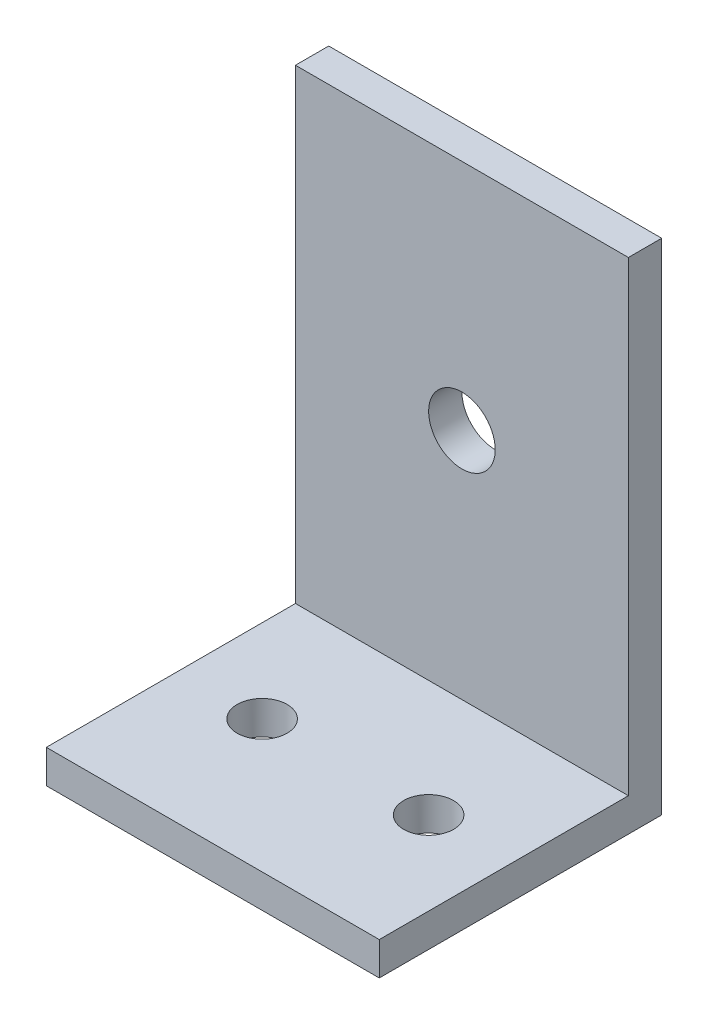
SolidWorks part; units mm, degrees
material "6063-O"
ref_plane "Front" through (0, 0, 0) normal (0, 0, 1) x (1, 0, 0)
ref_plane "Top" through (0, 0, 0) normal (0, 1, 0) x (1, 0, 0)
ref_plane "Right" through (0, 0, 0) normal (1, 0, 0) x (0, 0, -1)
sketch "草图1" plane through (0, 0, 0) normal (1, 0, 0) x (0, 0, -1)
  line L0 (0, 0) -> (0, 35)
  line L1 (0, 35) -> (3, 35)
  line L2 (3, 35) -> (3, -3)
  line L3 (0, 0) -> (-35, 0)
  line L4 (-35, 0) -> (-35, -3)
  line L5 (-35, -3) -> (3, -3)
  dimension "D1" = 35
  dimension "D2" = 3
  dimension "D3" = 38
  dimension "D4" = 35
extrude "凸台-拉伸1" add sketch "草图1" along normal blind 30
sketch "草图5" plane through (0, 0, 0) normal (0, 0, 1) x (1, 0, 0)
  line L0 (0, 20) -> (15, 35)
  line L1 (0, 35) -> (0, 0) construction
  line L2 (30, 35) -> (0, 35) construction
  line L3 (15, 35) -> (30, 20)
  line L4 (30, 35) -> (30, 0) construction
  line L5 (30, 20) -> (30, 35)
  line L6 (30, 35) -> (0, 35)
  line L7 (0, 35) -> (0, 20)
  line L8 (7.5, 27.5) -> (22.5, 27.5)
  line M3 (0, 35) -> (0, 0)
  line M5 (30, 0) -> (30, 35)
  line M6 (30, 35) -> (0, 35)
  dimension "D1" = 15
extrude "切除-拉伸4" [suppressed] cut sketch "草图5" against normal through all and the other way through all contours L0 M3 M6 | L0 L8 L3 | L3 M6 M5
fillet "圆角1" [suppressed] radius 3
sketch "草图6" plane through (0, 0, 0) normal (-1, 0, 0) x (0, 0, 1)
  line L1 (13.9641, -6.0203) -> (-8.0349, -6.0203)
  line L2 (13.9641, -6.0203) -> (13.9641, 37.9578)
  line L3 (13.9641, 37.9578) -> (-8.0349, 37.9578)
  line L4 (-8.0349, -6.0203) -> (-8.0349, 37.9578)
extrude "切除-拉伸5" cut sketch "草图6" against normal blind 10
sketch "草图7" plane through (0, 0, 0) normal (0, 1, 0) x (1, 0, 0)
  line L0 (0, -13.9641) -> (0, -35) construction
  line L1 (0, -13.9641) -> (30, -13.9641)
  line L2 (0, -13.9641) -> (0, -35)
  line L3 (0, -35) -> (30, -35)
  line L4 (30, -13.9641) -> (30, -35)
  line L5 (10, -13.9641) -> (0, -13.9641) construction
  line L6 (30, 0) -> (30, -35) construction
extrude "切除-拉伸6" cut sketch "草图7" against normal blind 10
sketch "草图8" plane through (0, 0, 0) normal (0, 1, 0) x (1, 0, 0)
  line L0 (10, -13.9641) -> (10, 0) construction
  line L3 (30, 0) -> (10, 0) construction
  circle A0 centre (15, -6) radius 1.5
  circle A1 centre (25, -6) radius 1.5
  dimension "D2" = 5
  dimension "D4" = 3
  dimension "D5" = 3
  dimension "D1" = 10
  dimension "D3" = 6
extrude "切除-拉伸7" cut sketch "草图8" against normal blind 10
sketch "草图9" plane through (0, 0, 0) normal (0, 1, 0) x (1, 0, 0)
  line L0 (10, -13.9641) -> (10, 0) construction
  line L1 (10, -13.9641) -> (30, -13.9641)
  line L2 (10, -13.9641) -> (10, 0)
  line L3 (10, 0) -> (30, 0)
  line L4 (30, -13.9641) -> (30, 0)
  line L5 (30, 0) -> (10, 0) construction
extrude "切除-拉伸8" cut sketch "草图9" against normal blind 1
sketch "草图10" plane through (0, 0, 0) normal (0, 0, 1) x (1, 0, 0)
  line L0 (30, 35) -> (10, 35) construction
  line L1 (10, -1) -> (30, -1)
  line L2 (10, -1) -> (10, 35)
  line L3 (10, 35) -> (30, 35)
  line L4 (30, -1) -> (30, 35)
extrude "切除-拉伸9" cut sketch "草图10" against normal blind 1
sketch "草图11" plane through (0, 35, 0) normal (0, 1, 0) x (1, 0, 0)
  line L0 (30, 1) -> (10, 1) construction
  line L1 (10, 1) -> (30, 1)
  line L2 (10, 1) -> (10, 3)
  line L3 (10, 3) -> (30, 3)
  line L4 (30, 1) -> (30, 3)
  line L5 (30, 3) -> (10, 3) construction
extrude "切除-拉伸10" cut sketch "草图11" against normal blind 8
sketch "草图12" plane through (0, 0, -3) normal (0, 0, -1) x (-1, 0, 0)
  circle A0 centre (-20, 13) radius 2
  dimension "D1" = 4
extrude "切除-拉伸11" cut sketch "草图12" against normal blind 8
